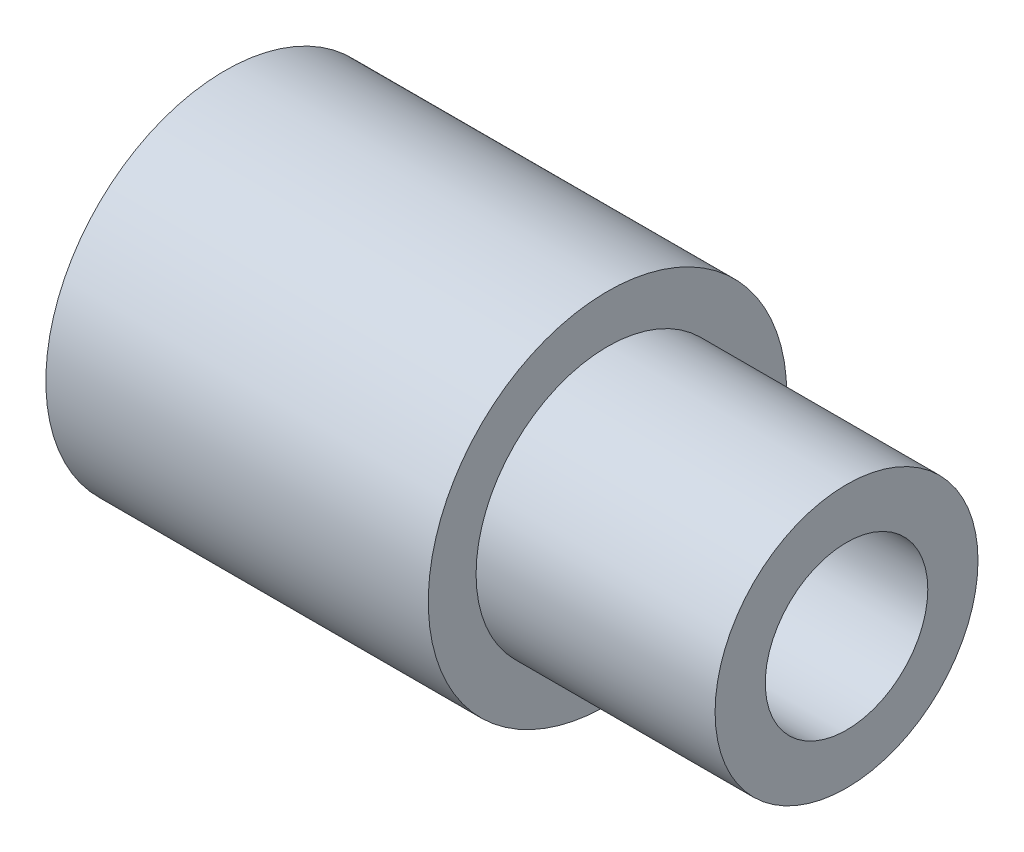
SolidWorks part; units mm, degrees
ref_plane "前视基准面" through (0, 0, 0) normal (0, 0, 1) x (1, 0, 0)
ref_plane "上视基准面" through (0, 0, 0) normal (0, 1, 0) x (1, 0, 0)
ref_plane "右视基准面" through (0, 0, 0) normal (1, 0, 0) x (0, 0, -1)
sketch "草图1" plane through (0, 0, 0) normal (1, 0, 0) x (0, 0, -1)
  circle A0 centre (0, 0) radius 1.7
  circle A1 centre (0, 0) radius 3.75
  dimension "D1" = 3.4
  dimension "D2" = 7.5
extrude "凸台-拉伸1" add sketch "草图1" along normal blind 13
sketch "草图2" plane through (13, 0, 0) normal (1, 0, 0) x (0, 0, -1)
  circle A0 centre (0, 0) radius 2.75
  circle A2 centre (0, 0) radius 4
  dimension "D1" = 5.5
  dimension "D2" = 8
extrude "切除-拉伸1" cut sketch "草图2" against normal blind 5
